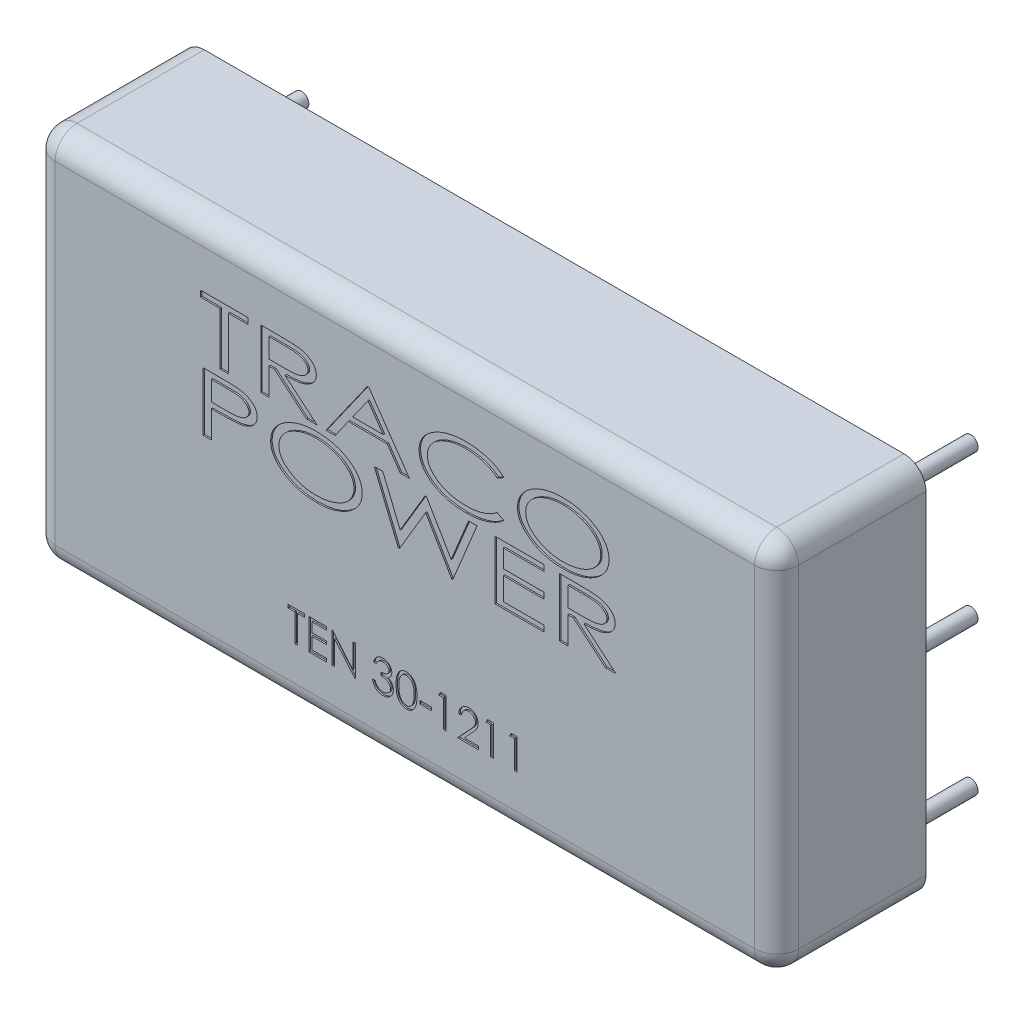
SolidWorks part; units mm, degrees
ref_plane "Front Plane" through (0, 0, 0) normal (0, 0, 1) x (1, 0, 0)
ref_plane "Top Plane" through (0, 0, 0) normal (0, 1, 0) x (1, 0, 0)
ref_plane "Right Plane" through (0, 0, 0) normal (1, 0, 0) x (0, 0, -1)
sketch "Sketch1" plane through (0, 0, 0) normal (0, 0, 1) x (1, 0, 0)
  line L1 (-25.4, -12.85) -> (25.4, -12.85)
  line L2 (-25.4, -12.85) -> (-25.4, 12.85)
  line L3 (-25.4, 12.85) -> (25.4, 12.85)
  line L4 (25.4, -12.85) -> (25.4, 12.85)
  line L5 (-25.4, -12.85) -> (25.4, 12.85) construction
  line L6 (-25.4, 12.85) -> (25.4, -12.85) construction
  point P0 (0, 0)
  dimension "D1" = 50.8
  dimension "D2" = 25.7
extrude "Boss-Extrude1" add sketch "Sketch1" along normal blind 10.2
fillet "Fillet1" radius 1.5 8 edges at (0, -12.85, 10.2) (-25.4, 0, 10.2) (0, 12.85, 10.2) (25.4, 0, 10.2) (-25.4, -12.85, 5.1) (25.4, -12.85, 5.1) (-25.4, 12.85, 5.1) (25.4, 12.85, 5.1)
sketch "Sketch2" plane through (0, 0, 10.2) normal (0, 0, 1) x (1, 0, 0)
  line L0 (0, -14.2048) -> (0, 14.7196) construction
  line L1 (14.405, 0) -> (-14.0825, 0) construction
  line L2 (-14.05, 4.7) -> (14.05, 4.7) construction
  line L3 (-14.5, 0.2) -> (14.5, 0.2) construction
  line L4 (-8, -9) -> (8, -9) construction
  text T0 "TRACO" font "Century Gothic" height 4
  text T1 "POWER" font "Century Gothic" height 4
  text T2 "TEN 30-1211" font "Century Gothic" height 2.1
  dimension "D1" = 28.1
  dimension "D2" = 29
  dimension "D3" = 0.2
  dimension "D4" = 4.7
  dimension "D5" = 16
  dimension "D6" = 9
extrude "Cut-Extrude1" cut sketch "Sketch2" against normal blind 0.1
sketch "Sketch3" plane through (0, 0, 0) normal (0, 0, -1) x (-1, 0, 0)
  line L1 (22.86, 10.16) -> (-22.86, 10.16) construction
  line L2 (22.86, 10.16) -> (22.86, -10.16) construction
  line L3 (22.86, -10.16) -> (-22.86, -10.16) construction
  line L4 (-22.86, 10.16) -> (-22.86, -10.16) construction
  line L5 (22.86, 10.16) -> (-22.86, -10.16) construction
  line L6 (22.86, -10.16) -> (-22.86, 10.16) construction
  circle A0 centre (-22.86, -10.16) radius 0.5
  circle A1 centre (-22.86, 0) radius 0.5
  circle A2 centre (-22.86, 10.16) radius 0.5
  circle A3 centre (22.86, 7.62) radius 0.5
  circle A4 centre (22.86, -2.54) radius 0.5
  circle A5 centre (22.86, -7.62) radius 0.5
  point P0 (0, 0)
  dimension "D1" = 1
  dimension "D2" = 20.32
  dimension "D3" = 2.54
  dimension "D4" = 5.08
  dimension "D5" = 15.24
  dimension "D6" = 45.72
extrude "Boss-Extrude2" add sketch "Sketch3" along normal blind 5.6
